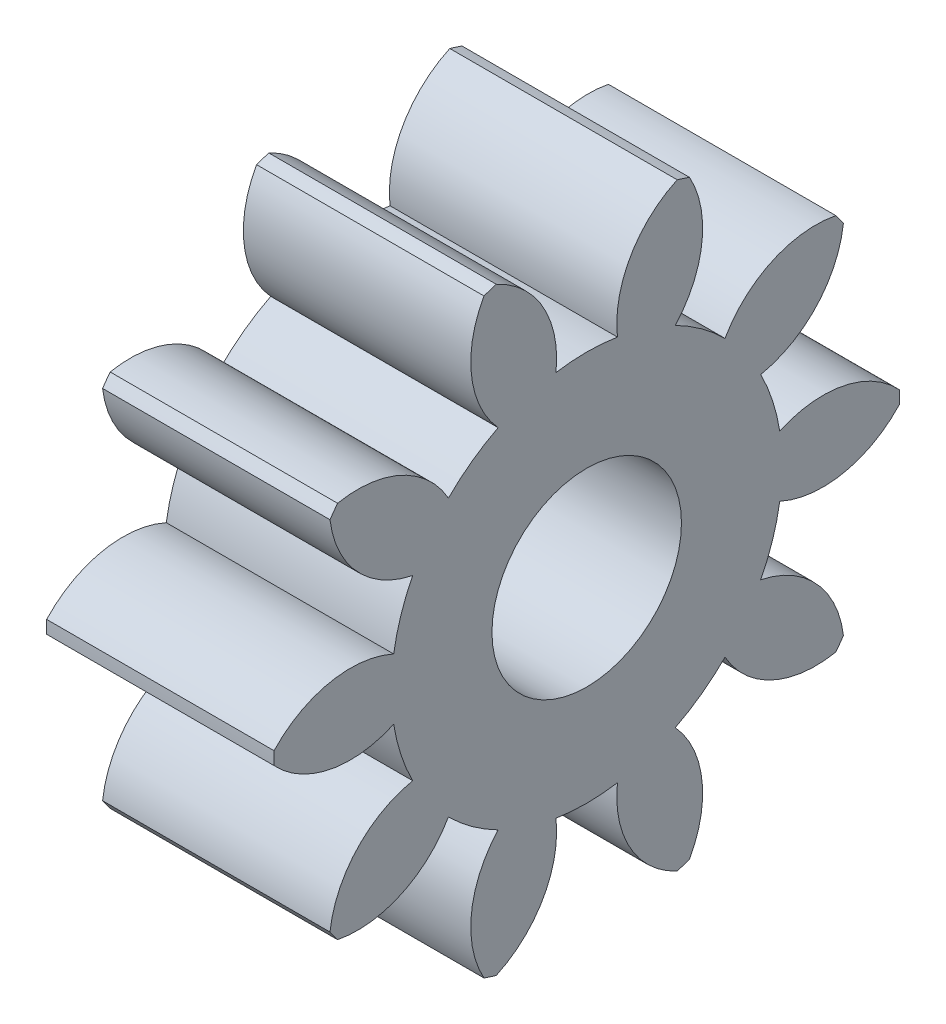
SolidWorks part; units mm, degrees
ref_plane "Plane1" through (0, 0, 0) normal (0, 0, 1) x (1, 0, 0)
ref_plane "Plane2" through (0, 0, 0) normal (0, 1, 0) x (1, 0, 0)
ref_plane "Plane3" through (0, 0, 0) normal (1, 0, 0) x (0, 0, -1)
sketch "HoldingSke" plane through (0, 0, 0) normal (0, 1, 0) x (1, 0, 0)
  line L0 (0, 0) -> (0.7162, -0.1263)
  line L1 (-15, 0) -> (100, 0) construction
  line L2 (0, 0) -> (-2.1039, 2.3779)
  line L3 (0, 0) -> (-11.863, 4.5341)
  line L4 (0, 0) -> (8.5048, 1.4996)
  line L5 (0, 0) -> (-46.8476, -17.4728)
  line L6 (0, 0) -> (-4.9738, -3.3558)
  line L7 (-2.1039, 2.3779) -> (8.6586, 51.2059)
  line L8 (-76.2, 54.61) -> (-75.3, 54.61)
  line L9 (-71.009, 38.7566) -> (-53.1078, 45.2721)
  line L10 (-76.2, 71.12) -> (104.1128, 71.12)
  line L11 (0, 0) -> (-6, 0)
  line L12 (-76.2, 101.6) -> (-76.151, 101.6)
  line L13 (24.9733, 27.94) -> (52.9518, 28.4284)
  line L14 (24.9733, 27.94) -> (24.9743, 27.94)
  line L15 (24.9733, 27.94) -> (100.4006, 29.5858)
  line L16 (-63.627, -1.375) -> (-12.827, -1.375)
  circle A0 centre (0, 0) radius 2.5
  circle A1 centre (0, 0) radius 5.1553
  circle A2 centre (0, 0) radius 37.5
  circle A3 centre (0, 0) radius 2.5
  dimension "MHD" = 10.3105
  dimension "Hub_dia" = 75
  dimension "Bore" = 5
  dimension "MBD" = 5
  dimension "Num_teeth" = 10
  dimension "Pitch" = 0.7273
  dimension "Overall_len" = 50
  dimension "Show_teeth" = 10
  dimension "Thickness" = 6
  dimension "OAL" = 50.0001
  dimension "T_dim" = 0.9
  dimension "Ap" = 20
  dimension "H" = 19.05
  dimension "Pitch_radius" = 180.3128
  dimension "Width" = 6
  dimension "Backlash" = 0.049
  dimension "Addendum_fac" = 1
  dimension "Dedendum_fac" = 1.25
  dimension "Clearance_fac" = 0.25
  dimension "Dedendum_add" = 0.001
  dimension "Module" = 1.375
sketch "BasProSke" plane through (0, 0, 0) normal (0, 1, 0) x (1, 0, 0)
  line L0 (-10, 0) -> (60, 0) construction
  line L1 (0, 0) -> (0, 8.25)
  line L2 (0, 0) -> (6, 0)
  line L3 (6, 0) -> (6, 8.25)
  line L4 (6, 8.25) -> (0, 8.25)
  dimension "Thickness" = 6
  dimension "Diameter" = 16.5
revolve "Base-Revolve" add sketch "BasProSke" angle 360 about L0
sketch "TooCutSke" plane through (0, 0, 0) normal (1, 0, 0) x (0, 0, -1)
  line L1 (0, 0) -> (0, 107) construction
  line L2 (0, 0) -> (-1.1611, 6.7762) construction
  line L3 (0, 0) -> (-4.2047, 12.9408) construction
  line L4 (-1.1611, 6.7762) -> (-2.1024, 6.4704) construction
  arc A0 (0.8108, 5.0911) -> (-0.8108, 5.0911) centre (0, 0) ccw
  arc A1 (2.4218, 7.9131) -> (-2.4218, 7.9131) centre (0, 0) ccw
  circle A2 centre (0, 0) radius 6.875 construction
  circle A3 centre (0, 0) radius 6.4604 construction
  arc A4 (-0.8108, 5.0911) -> (-2.4218, 7.9131) centre (-3.5431, 5.4021) ccw
  arc A5 (2.4218, 7.9131) -> (0.8108, 5.0911) centre (3.5431, 5.4021) ccw
  dimension "Root_dia" = 10.3105
  dimension "Overcut_dia" = 16.5508
  dimension "Pitch_dia" = 13.75
  dimension "Base_dia" = 12.9208
  dimension "Flank_rad" = 2.75
  dimension "Half_ang" = 18
  dimension "Half_CT" = 0.9897
extrude "ToothCut" cut sketch "TooCutSke" along normal through all
fillet "Breaks" [suppressed] radius 0.0275
fillet "RootFillets" [suppressed] radius 0.3448
pattern_circular "TeethCuts" count 10 every 36 about axis through (-10, 0, 0) along (1, 0, 0) of "ToothCut", "RootFillets", "Breaks"
sketch "HubNeaOneSke" plane through (0, 0, 0) normal (-1, 0, 0) x (0, 0, 1)
  circle A0 centre (0, 0) radius 5.1553
  dimension "Diameter" = 10.3105
extrude "HubNearOne" [suppressed] add sketch "HubNeaOneSke" along normal blind 44.0001
sketch "HubNeaBotSke" plane through (0, 0, 0) normal (-1, 0, 0) x (0, 0, 1)
  circle A0 centre (0, 0) radius 5.1553
  dimension "Diameter" = 10.3105
extrude "HubNearBoth" [suppressed] add sketch "HubNeaBotSke" along normal blind 22
ref_plane "FarPln" through (6, 0, 0) normal (1, 0, 0) x (0, 0, -1)
sketch "HubFarSke" plane through (6, 0, 0) normal (1, 0, 0) x (0, 0, -1)
  circle A0 centre (0, 0) radius 5.1553
  dimension "Diameter" = 10.3105
extrude "HubFar" [suppressed] add sketch "HubFarSke" along normal blind 22
sketch "BorSke" plane through (0, 0, 0) normal (1, 0, 0) x (0, 0, -1)
  circle A0 centre (0, 0) radius 2.5
  dimension "Diameter" = 5
extrude "Bore" cut sketch "BorSke" along normal mid plane 100.0001
sketch "KeySke" plane through (0, 0, 0) normal (1, 0, 0) x (0, 0, -1)
  line L0 (-1, 0) -> (-1, 3.4)
  line L1 (-1, 3.4) -> (1, 3.4)
  line L2 (1, 3.4) -> (1, 0)
  line L3 (0, 0) -> (0, 34) construction
  line L4 (-1, 0) -> (1, 0)
  dimension "Offset" = 3.4
  dimension "Width" = 2
extrude "Keyway" [suppressed] cut sketch "KeySke" along normal mid plane 100.0001
pattern_circular "Keyway2" [suppressed] count 2 every 90 about axis through (-10, 0, 0) along (1, 0, 0)
equation "' \"Module@HoldingSke\" = 6.35"
equation "' \"Num_teeth@HoldingSke\" = 12"
equation "' \"Ap@HoldingSke\" =  20"
equation "' \"Ap@HoldingSke\" = 20"
equation "' \"Width@HoldingSke\" = 0.5 * 25.4"
equation "' \"Hub_dia@HoldingSke\"= 1 * 25.4"
equation "' \"Hub_dia@HoldingSke\" = 1 * 25.4"
equation "' \"Overall_len@HoldingSke\" = 1.0 * 25.4"
equation "' \"Bore@HoldingSke\" = 0.75 * 25.4"
equation "' \"T_dim@HoldingSke\" = 0.1 * 25.4"
equation "' \"Width@KeySke\" = 0.25 * 25.4"
equation "' \"Show_teeth@HoldingSke\" = 13"
equation "' \"Backlash@HoldingSke\" = 0.009 * 25.4"
equation "' \"Addendum_fac@HoldingSke\" = 1.0"
equation "' \"Dedendum_fac@HoldingSke\" = 1.25"
equation "' \"Dedendum_add@HoldingSke\" = 0.00005 * 25.4"
equation "' \"Clearance_fac@HoldingSke\" = 0.25"
equation "\"Pitch@HoldingSke\" = 1 / \"Module@HoldingSke\""
equation "\"Overcut_dia@TooCutSke\" = (\"Num_teeth@HoldingSke\" + 2 * \"Addendum_fac@HoldingSke\") / \"Pitch@HoldingSke\" + 0.002 * 25.4"
equation "\"Pitch_dia@TooCutSke\" = \"Num_teeth@HoldingSke\" / \"Pitch@HoldingSke\""
equation "\"Base_dia@TooCutSke\" = \"Num_teeth@HoldingSke\" / \"Pitch@HoldingSke\" * cos((\"Ap@HoldingSke\"  * 3.14159265 / 180))"
equation "\"Root_dia@TooCutSke\" = (\"Num_teeth@HoldingSke\" + 2) / \"Pitch@HoldingSke\" - 2 * (\"Addendum_fac@HoldingSke\" + \"Dedendum_fac@HoldingSke\") / \"Pitch@HoldingSke\" - \"Dedendum_add@HoldingSke\" * 2"
equation "\"Half_ang@TooCutSke\" = 180 / \"Num_teeth@HoldingSke\""
equation "\"Half_CT@TooCutSke\" = \"Num_teeth@HoldingSke\" / \"Pitch@HoldingSke\" * sin((3.14159265 / 2 / \"Num_teeth@HoldingSke\")) / 2 - 7 * \"Backlash@HoldingSke\" / 4"
equation "\"Flank_rad@TooCutSke\" = \"Num_teeth@HoldingSke\" / \"Pitch@HoldingSke\" / 5"
equation "\"Radius@RootFillets\" = \"Clearance_fac@HoldingSke\" / \"Pitch@HoldingSke\" + \"Dedendum_add@HoldingSke\""
equation "\"Break_rad@Breaks\" = 0.02 / \"Pitch@HoldingSke\""
equation "\"Thickness@HoldingSke\" = \"Width@HoldingSke\""
equation "\"OAL@HoldingSke\" = \"Thickness@HoldingSke\""
equation "\"MHD@HoldingSke\" = (\"Num_teeth@HoldingSke\" + 2) / \"Pitch@HoldingSke\" - 2 * (\"Addendum_fac@HoldingSke\" + \"Dedendum_fac@HoldingSke\")  / \"Pitch@HoldingSke\" - \"Dedendum_add@HoldingSke\" * 2"
equation "\"MBD@HoldingSke\" = (\"Num_teeth@HoldingSke\" + 2) / \"Pitch@HoldingSke\" - 2 * (\"Addendum_fac@HoldingSke\" + \"Dedendum_fac@HoldingSke\")  / \"Pitch@HoldingSke\" - \"Dedendum_add@HoldingSke\" * 2 - 0.002 * 25.4"
equation "\"MHD@HoldingSke\" = ((sgn( \"MHD@HoldingSke\" - \"Hub_dia@HoldingSke\" )-1)*( \"MHD@HoldingSke\" - \"Hub_dia@HoldingSke\" ))/-2+ \"Hub_dia@HoldingSke\""
equation "\"MBD@HoldingSke\" = ((sgn( \"MBD@HoldingSke\" - \"Bore@HoldingSke\" )-1)*( \"MBD@HoldingSke\" - \"Bore@HoldingSke\" ))/-2+ \"Bore@HoldingSke\""
equation "\"OAL@HoldingSke\" = ((sgn( \"OAL@HoldingSke\" - \"Overall_len@HoldingSke\" )+1)*( \"OAL@HoldingSke\" - \"Overall_len@HoldingSke\" ))/2 + \"Overall_len@HoldingSke\" + 0.000002 * 25.4"
equation "\"Num_teeth@TeethCuts\" = int( \"Show_teeth@HoldingSke\" ) + 1"
equation "\"Num_teeth@TeethCuts\" = ((sgn( \"Num_teeth@TeethCuts\" - \"Num_teeth@HoldingSke\" )-1)*( \"Num_teeth@TeethCuts\" - \"Num_teeth@HoldingSke\" ))/-2+ \"Num_teeth@HoldingSke\""
equation "\"Num_teeth@TeethCuts\" = ((sgn( \"Num_teeth@TeethCuts\" - 2.0)+1)*( \"Num_teeth@TeethCuts\" - 2.0))/2 +2.0"
equation "\"Angle@TeethCuts\" = 360.0 / \"Num_teeth@HoldingSke\""
equation "\"Diameter@BasProSke\" = (\"Num_teeth@HoldingSke\" + 2 * \"Addendum_fac@HoldingSke\") / \"Pitch@HoldingSke\""
equation "\"Thickness@BasProSke\"  = \"Thickness@HoldingSke\""
equation "' \"Fillet_rad@BasProSke\" =  \"Thickness@HoldingSke\" * 0.05"
equation "' \"Fillet_rad@BasProSke\" = \"Thickness@HoldingSke\" * 0.05"
equation "\"MHD@HoldingSke\" = ((sgn( \"MHD@HoldingSke\" - \"Root_dia@TooCutSke\" )-1)*( \"MHD@HoldingSke\" - \"Root_dia@TooCutSke\" ))/-2+ \"Root_dia@TooCutSke\""
equation "\"Diameter@HubNeaOneSke\" = \"MHD@HoldingSke\""
equation "\"Length@HubNearOne\" = \"OAL@HoldingSke\" - \"Thickness@BasProSke\""
equation "\"Diameter@HubNeaBotSke\" = \"MHD@HoldingSke\""
equation "\"Length@HubNearBoth\" = ( \"OAL@HoldingSke\" - \"Thickness@BasProSke\" ) / 2.0"
equation "\"Thickness@FarPln\" = \"Thickness@BasProSke\""
equation "\"Diameter@HubFarSke\" = \"MHD@HoldingSke\""
equation "\"Length@HubFar\" = ( \"OAL@HoldingSke\" - \"Thickness@BasProSke\" ) / 2.0"
equation "\"Diameter@BorSke\" = \"MBD@HoldingSke\""
equation "\"D1@Bore\" = \"OAL@HoldingSke\" * 2.0"
equation "\"D1@Keyway\" = \"OAL@HoldingSke\" * 2.0"
equation "\"Offset@KeySke\" = \"T_dim@HoldingSke\" + \"MBD@HoldingSke\" / 2.0"
